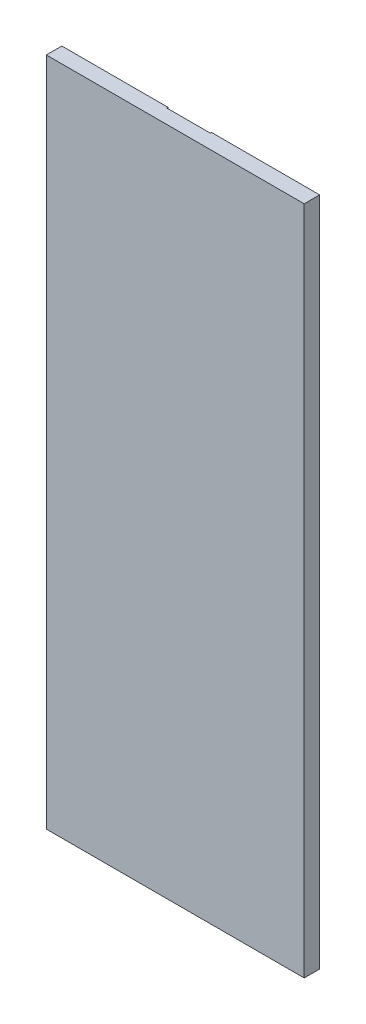
SolidWorks part; units mm, degrees
ref_plane "Plane1" through (0, 0, 0) normal (0, 0, 1) x (1, 0, 0)
ref_plane "Plane2" through (0, 0, 0) normal (0, 1, 0) x (1, 0, 0)
ref_plane "Plane3" through (0, 0, 0) normal (1, 0, 0) x (0, 0, -1)
sketch "Sketch1" plane through (0, 0, 0) normal (0, 1, 0) x (1, 0, 0)
  line L1 (0, 0) -> (250, 0)
  line L2 (0, 0) -> (0, 15)
  line L3 (0, 15) -> (250, 15)
  line L4 (250, 0) -> (250, 15)
  dimension "D1" = 15
  dimension "D2" = 250
extrude "Boss-Extrude1" add sketch "Sketch1" along normal blind 650
sketch "Sketch3" plane through (0, 0, -15) normal (0, 0, -1) x (-1, 0, 0)
  line L1 (-145.15, 650) -> (-102.85, 650)
  line L2 (-145.15, 650) -> (-145.15, 593)
  line L3 (-145.15, 593) -> (-102.85, 593)
  line L4 (-102.85, 650) -> (-102.85, 593)
  line L7 (-250, 650) -> (0, 650) construction
  line L8 (-250, 650) -> (-250, 0) construction
  dimension "D1" = 104.85
  dimension "D2" = 42.3
  dimension "D3" = 57
  dimension "D4" = 57
extrude "Cut-Extrude2" cut sketch "Sketch3" against normal blind 1.15
